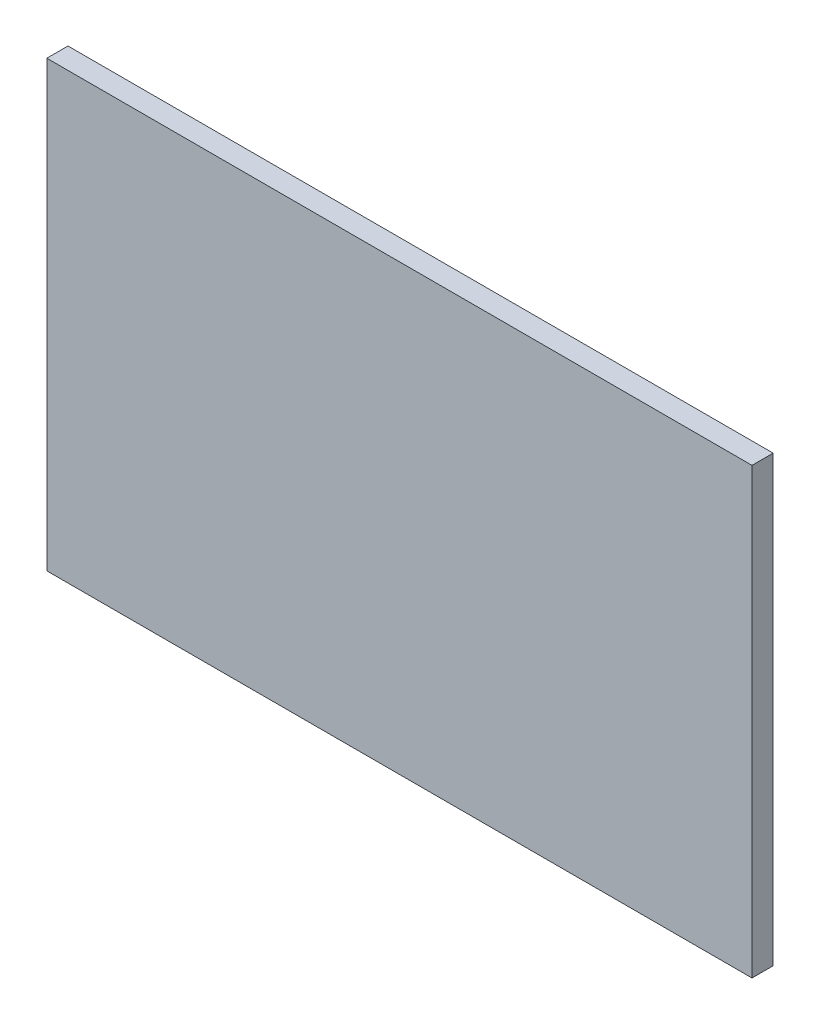
SolidWorks part; units mm, degrees
ref_plane "Front" through (0, 0, 0) normal (0, 0, 1) x (1, 0, 0)
ref_plane "Top" through (0, 0, 0) normal (0, 1, 0) x (1, 0, 0)
ref_plane "Right" through (0, 0, 0) normal (1, 0, 0) x (0, 0, -1)
sketch "Sketch1" plane through (0, 0, 0) normal (0, 0, 1) x (1, 0, 0)
  line L1 (557.5, 351) -> (-557.5, 351)
  line L2 (557.5, 351) -> (557.5, -351)
  line L3 (557.5, -351) -> (-557.5, -351)
  line L4 (-557.5, 351) -> (-557.5, -351)
  line L5 (557.5, 351) -> (-557.5, -351) construction
  line L6 (557.5, -351) -> (-557.5, 351) construction
  point P0 (0, 0)
  dimension "D1" = 702
  dimension "D2" = 1115
extrude "Boss-Extrude1" add sketch "Sketch1" along normal blind 33.45
